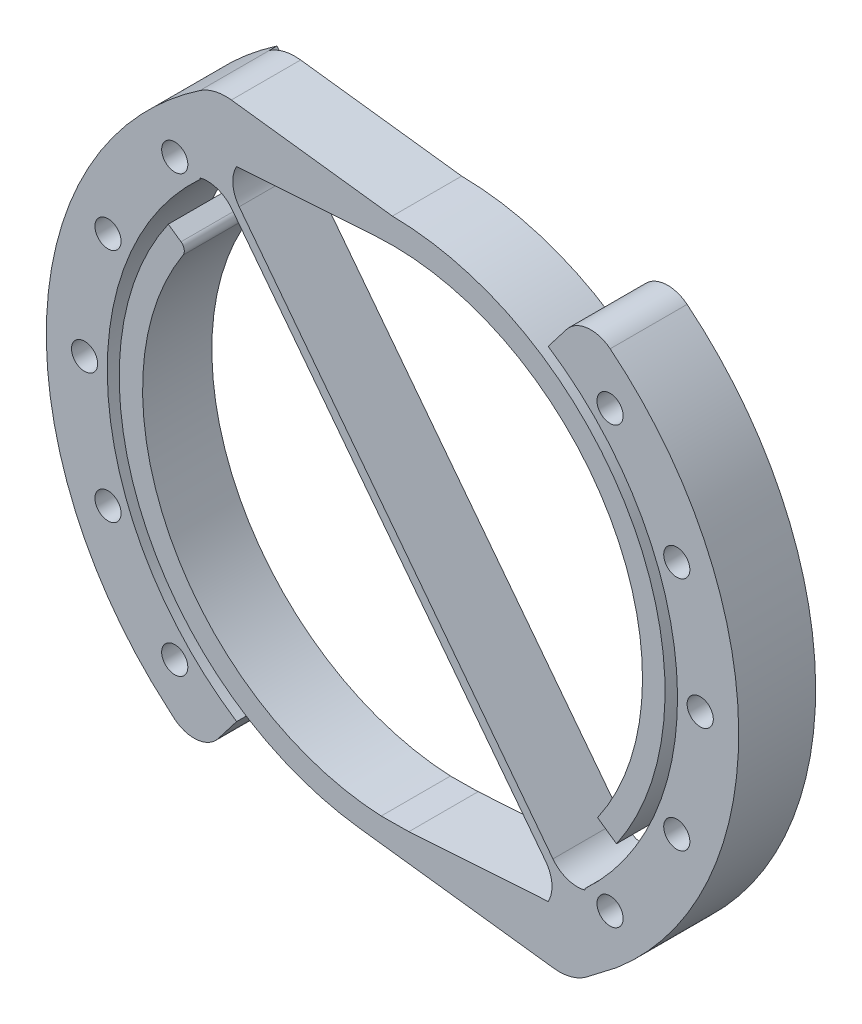
SolidWorks part; units mm, degrees
ref_plane "Front Plane" through (0, 0, 0) normal (0, 0, 1) x (1, 0, 0)
ref_plane "Top Plane" through (0, 0, 0) normal (0, 1, 0) x (1, 0, 0)
ref_plane "Right Plane" through (0, 0, 0) normal (1, 0, 0) x (0, 0, -1)
sketch "Sketch2" plane through (0, 0, 0) normal (0, 0, 1) x (1, 0, 0)
  line L0 (2.7131, 1.3894) -> (1.5281, -0.151)
  line L1 (24.1427, 34.165) -> (22.9576, 32.6245)
  line L2 (-1.7539, -0.096) -> (-1.3149, -0.4865)
  line L3 (0.3353, 30.7134) -> (0.3353, 30.7953)
  line L4 (-0.8992, 26.5823) -> (-1.7256, 27.1585)
  line L5 (12.1065, 0.7729) -> (13.9058, 0.7919)
  line L6 (13.9058, 0.7919) -> (22.9576, 1.3894)
  line L7 (2.4041, 30.0741) -> (22.791, 3.574)
  line L8 (10.6412, -0.6072) -> (23.2979, -2.1838)
  line L9 (25.3353, -1.7013) -> (27.4264, -0.096)
  line L10 (12.8354, 34.8945) -> (2.3728, 36.1978)
  line L11 (11.7649, 33.2221) -> (2.7131, 32.6245)
  line L12 (26.1659, 7.7134) -> (27.3964, 6.8555)
  line L13 (2.8797, 30.44) -> (23.2666, 3.9399)
  line L14 (25.3353, 3.3005) -> (25.3353, 3.2187)
  arc A0 (0.3353, 30.7134) -> (2.7131, 1.3894) centre (12.973, 16.9798) ccw
  arc A1 (22.9576, 32.6245) -> (25.3353, 3.3005) centre (12.6985, 17.0343) cw
  arc A2 (-3.4783, 32.4688) -> (-1.7539, -0.096) centre (12.8066, 17.0031) ccw
  arc A3 (26.9846, 34.5013) -> (27.4264, -0.096) centre (12.8631, 17.0195) cw
  arc A4 (-3.4783, 32.4688) -> (0.3353, 35.7153) centre (13.6919, 16.1623) cw
  arc A5 (2.4041, 30.0741) -> (0.3353, 30.7953) centre (0.8189, 28.8546) ccw
  arc A6 (-0.8992, 26.5823) -> (-0.766, 25.8996) centre (-1.1851, 26.1721) cw
  arc A7 (-1.3149, -0.4865) -> (1.5281, -0.151) centre (-0.0571, 1.0685) ccw
  arc A8 (10.6412, -0.6072) -> (-1.7256, 27.1585) centre (12.8354, 17.007) cw
  arc A9 (-0.766, 25.8996) -> (12.1065, 0.7729) centre (12.877, 17.0283) ccw
  arc A10 (22.791, 3.574) -> (22.9576, 1.3894) centre (21.2058, 2.3545) cw
  arc A11 (25.3353, -1.7013) -> (23.2979, -2.1838) centre (23.6687, 0.7932) cw
  arc A12 (24.1427, 34.165) -> (26.9846, 34.5013) centre (25.7278, 32.9455) cw
  arc A13 (0.3353, 35.7153) -> (2.3728, 36.1978) centre (2.0019, 33.2209) cw
  arc A14 (2.8797, 30.44) -> (2.7131, 32.6245) centre (4.4649, 31.6595) cw
  arc A15 (12.8354, 34.8945) -> (27.3964, 6.8555) centre (12.6558, 17.0009) cw
  arc A16 (11.7649, 33.2221) -> (26.1659, 7.7134) centre (12.8354, 17.007) cw
  arc A17 (23.2666, 3.9399) -> (25.3353, 3.2187) centre (24.8518, 5.1594) ccw
  dimension "D1" = 18.6634
  dimension "D2" = 18.6629
  dimension "D3" = 22.4585
  dimension "D4" = 22.4729
  dimension "D5" = 23.6795
  dimension "D6" = 2
  dimension "D7" = 0.5
  dimension "D8" = 2
  dimension "D9" = 17.7504
  dimension "D10" = 16.2736
  dimension "D11" = 3
  dimension "D12" = 3
  dimension "D13" = 17.8945
  dimension "D14" = 16.2504
  dimension "D15" = 2
  dimension "D16" = 0.3353
  dimension "D17" = 0.8189
  dimension "D18" = 1.5281
  dimension "D19" = 2.0019
  dimension "D20" = 2.3728
  dimension "D21" = 2.4041
  dimension "D22" = 2.7131
  dimension "D23" = 2.8797
  dimension "D24" = 10.6412
  dimension "D25" = 11.7649
  dimension "D26" = 12.6558
  dimension "D27" = 12.1065
  dimension "D28" = 12.6985
  dimension "D29" = 12.8066
  dimension "D30" = 12.8631
  dimension "D31" = 12.877
  dimension "D32" = 12.973
  dimension "D33" = 13.6919
  dimension "D34" = 13.9058
  dimension "D35" = 21.2058
  dimension "D36" = 23.2979
  dimension "D37" = 25.7278
  dimension "D38" = 26.1659
  dimension "D39" = 27.4264
  dimension "D40" = 0.766
  dimension "D41" = 0.7729
  dimension "D55" = 1.3149
extrude "Boss-Extrude1" add sketch "Sketch2" along normal mid plane 4.5
sketch "Sketch3" plane through (0, 0, -2.25) normal (0, 0, -1) x (-1, 0, 0)
  line L0 (-25.3353, 3.2187) -> (-22.9576, 1.3894)
  line L1 (-22.9576, 1.3894) -> (-25.3353, -1.7013)
  line L2 (-0.3353, 30.7953) -> (-2.7131, 32.6245)
  line L3 (-2.7131, 32.6245) -> (-0.3353, 35.7153)
  line L15 (-2.7131, 1.3894) -> (-1.5281, -0.151)
  line L16 (1.3149, -0.4865) -> (1.7539, -0.096)
  line L17 (-2.3728, 36.1978) -> (-12.8354, 34.8945)
  line L18 (-27.3964, 6.8555) -> (-26.1659, 7.7134)
  line L19 (-11.7649, 33.2221) -> (-2.7131, 32.6245)
  line L20 (-2.8797, 30.44) -> (-23.2666, 3.9399)
  line L21 (-25.3353, 3.2187) -> (-25.3353, 3.3005)
  line L22 (-22.9576, 32.6245) -> (-24.1427, 34.165)
  line L23 (-27.4264, -0.096) -> (-25.3353, -1.7013)
  line L24 (-23.2979, -2.1838) -> (-10.6412, -0.6072)
  line L25 (1.7256, 27.1585) -> (0.8992, 26.5823)
  line L26 (-12.1065, 0.7729) -> (-13.9058, 0.7919)
  line L27 (-13.9058, 0.7919) -> (-22.9576, 1.3894)
  line L28 (-22.791, 3.574) -> (-2.4041, 30.0741)
  line L29 (-0.3353, 30.7953) -> (-0.3353, 30.7134)
  line L30 (-2.7131, 1.3894) -> (-1.5281, -0.151)
  line L31 (1.3149, -0.4865) -> (1.7539, -0.096)
  line L36 (-25.3353, 3.2187) -> (-25.3353, 3.3005)
  line L37 (-22.9576, 32.6245) -> (-24.1427, 34.165)
  line L38 (-27.4264, -0.096) -> (-25.3353, -1.7013)
  line L44 (-0.3353, 30.7953) -> (-0.3353, 30.7134)
  arc A18 (-2.7131, 1.3894) -> (-0.3353, 30.7134) centre (-12.973, 16.9798) ccw
  arc A19 (-1.5281, -0.151) -> (1.3149, -0.4865) centre (0.0571, 1.0685) ccw
  arc A20 (1.7539, -0.096) -> (3.4783, 32.4688) centre (-12.8066, 17.0031) ccw
  arc A21 (3.4783, 32.4688) -> (-0.3353, 35.7153) centre (-13.6919, 16.1623) ccw
  arc A22 (-0.3353, 35.7153) -> (-2.3728, 36.1978) centre (-2.0019, 33.2209) ccw
  arc A23 (-12.8354, 34.8945) -> (-27.3964, 6.8555) centre (-12.6558, 17.0009) ccw
  arc A24 (-11.7649, 33.2221) -> (-26.1659, 7.7134) centre (-12.8354, 17.007) ccw
  arc A25 (-2.8797, 30.44) -> (-2.7131, 32.6245) centre (-4.4649, 31.6595) ccw
  arc A26 (-25.3353, 3.2187) -> (-23.2666, 3.9399) centre (-24.8518, 5.1594) ccw
  arc A27 (-22.9576, 32.6245) -> (-25.3353, 3.3005) centre (-12.6985, 17.0343) ccw
  arc A28 (-24.1427, 34.165) -> (-26.9846, 34.5013) centre (-25.7278, 32.9455) ccw
  arc A29 (-26.9846, 34.5013) -> (-27.4264, -0.096) centre (-12.8631, 17.0195) ccw
  arc A30 (-25.3353, -1.7013) -> (-23.2979, -2.1838) centre (-23.6687, 0.7932) ccw
  arc A31 (-10.6412, -0.6072) -> (1.7256, 27.1585) centre (-12.8354, 17.007) ccw
  arc A32 (0.8992, 26.5823) -> (0.766, 25.8996) centre (1.1851, 26.1721) ccw
  arc A33 (-12.1065, 0.7729) -> (0.766, 25.8996) centre (-12.877, 17.0283) ccw
  arc A34 (-22.791, 3.574) -> (-22.9576, 1.3894) centre (-21.2058, 2.3545) ccw
  arc A35 (-0.3353, 30.7953) -> (-2.4041, 30.0741) centre (-0.8189, 28.8546) ccw
  arc A36 (-2.7131, 1.3894) -> (-0.3353, 30.7134) centre (-12.973, 16.9798) ccw
  arc A37 (-1.5281, -0.151) -> (1.3149, -0.4865) centre (0.0571, 1.0685) ccw
  arc A38 (1.7539, -0.096) -> (3.4783, 32.4688) centre (-12.8066, 17.0031) ccw
  arc A39 (3.4783, 32.4688) -> (-0.3353, 35.7153) centre (-13.6919, 16.1623) ccw
  arc A45 (-22.9576, 32.6245) -> (-25.3353, 3.3005) centre (-12.6985, 17.0343) ccw
  arc A46 (-24.1427, 34.165) -> (-26.9846, 34.5013) centre (-25.7278, 32.9455) ccw
  arc A47 (-26.9846, 34.5013) -> (-27.4264, -0.096) centre (-12.8631, 17.0195) ccw
  dimension "D1" = 0
extrude "Boss-Extrude2" add sketch "Sketch3" along normal blind 0.5
sketch "Sketch5" plane through (0, 0, -2.75) normal (0, 0, -1) x (-1, 0, 0)
  line L12 (-25.3353, 3.2187) -> (-25.3353, 3.3005) construction
  line L25 (-2.7131, 32.6245) -> (-0.3353, 35.7153) construction
  line L26 (-2.7131, 1.3894) -> (-1.528, -0.151) construction
  line L27 (-2.7131, 1.3894) -> (-0.3353, 3.2186) construction
  line L28 (-0.3353, 3.2186) -> (-0.3353, 3.3005) construction
  line L29 (-0.3353, 30.7953) -> (-0.3353, 30.7134) construction
  line L30 (-0.3353, 30.7953) -> (-2.7131, 32.6245) construction
  line L31 (-24.1426, 34.1649) -> (-22.9576, 32.6245) construction
  line L32 (-22.9576, 32.6245) -> (-25.3353, 30.7953) construction
  line L33 (-25.3353, 30.7953) -> (-25.3353, 30.7134) construction
  line L34 (-25.3353, 3.3005) -> (-25.3353, 3.2186) construction
  line L35 (-25.3353, 3.2186) -> (-22.9576, 1.3894) construction
  line L36 (-22.9576, 1.3894) -> (-25.3353, -1.7013) construction
  arc A34 (-0.3353, 35.7153) -> (1.315, -0.4865) centre (-12.8353, 17.007) cw construction
  arc A35 (-1.528, -0.151) -> (1.315, -0.4865) centre (0.0572, 1.0685) ccw construction
  arc A36 (-0.3353, 3.3005) -> (-0.3353, 30.7134) centre (-12.8353, 17.007) ccw construction
  circle A37 centre (1.3068, 31.1491) radius 0.85
  circle A38 centre (5.6423, 24.6606) radius 0.85
  circle A39 centre (7.1647, 17.007) radius 0.85
  circle A40 centre (5.6423, 9.3533) radius 0.85
  circle A41 centre (1.3068, 2.8648) radius 0.85
  arc A42 (-25.3353, 30.7134) -> (-25.3353, 3.3005) centre (-12.8353, 17.007) ccw construction
  arc A43 (-26.9856, 34.5004) -> (-25.3353, -1.7013) centre (-12.8353, 17.007) ccw construction
  arc A44 (-26.9856, 34.5004) -> (-24.1426, 34.1649) centre (-25.7278, 32.9454) cw construction
  circle A45 centre (-26.9775, 2.8648) radius 0.85
  circle A46 centre (-31.3129, 9.3533) radius 0.85
  circle A47 centre (-32.8353, 17.007) radius 0.85
  circle A48 centre (-31.3129, 24.6606) radius 0.85
  circle A49 centre (-26.9775, 31.1491) radius 0.85
  arc A50 (-23.8071, 33.7288) -> (-23.8071, 0.2851) centre (-12.8353, 17.007) ccw construction
  arc A51 (-1.8635, 0.2851) -> (-1.8635, 33.7288) centre (-12.8353, 17.007) ccw construction
  point P23 (0, 0)
  point P48 (0, 0)
extrude "Cut-Extrude1" cut sketch "Sketch5" against normal through all both and the other way through all contours A48 | A47 | A46 | A45 | A41 | A38 | A37 | A49 | A40 | A39
